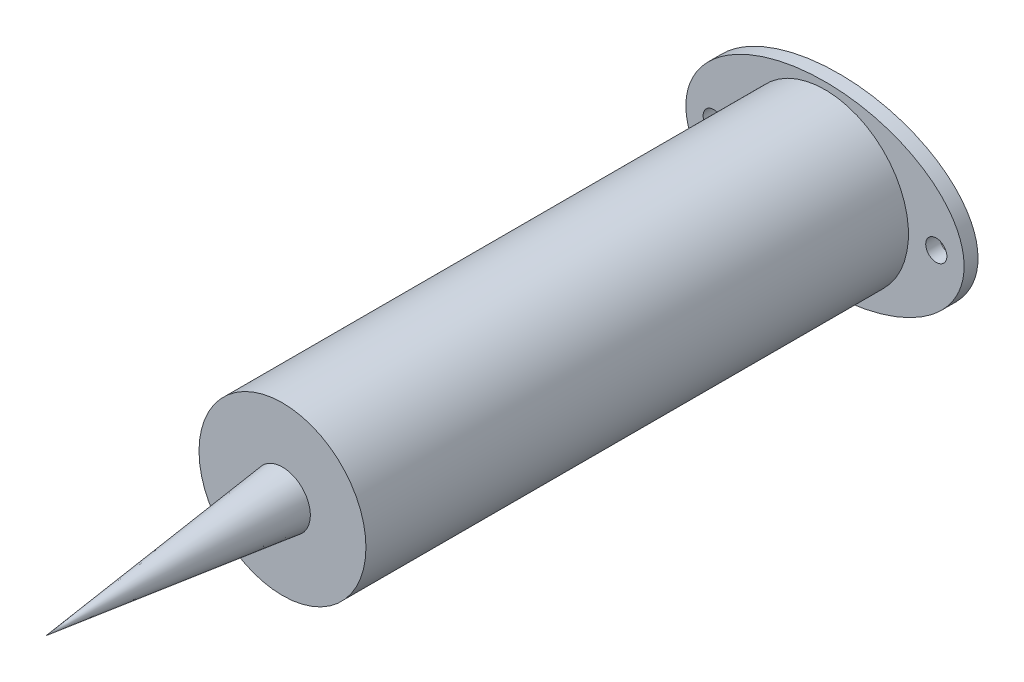
SolidWorks part; units mm, degrees
ref_plane "Front Plane" through (0, 0, 0) normal (0, 0, 1) x (1, 0, 0)
ref_plane "Top Plane" through (0, 0, 0) normal (0, 1, 0) x (1, 0, 0)
ref_plane "Right Plane" through (0, 0, 0) normal (1, 0, 0) x (0, 0, -1)
sketch "Sketch1" plane through (0, 0, 0) normal (0, 0, 1) x (1, 0, 0)
  circle A0 centre (0, 0) radius 17.4625
  circle A1 centre (0, 0) radius 19.05
  dimension "D1" = 34.925
  dimension "D2" = 38.1
extrude "Boss-Extrude1" add sketch "Sketch1" along normal blind 123.825
sketch "Sketch2" plane through (0, 0, 0) normal (0, 0, -1) x (-1, 0, 0)
  line L0 (0, 0) -> (-33.793, 0) construction
  line L1 (-33.793, 0) -> (0, 0) construction
  line L2 (0, 0) -> (0, 22.7795) construction
  line L3 (0, 0) -> (25.4, 0) construction
  circle A0 centre (0, 0) radius 17.4625
  circle A1 centre (0, 0) radius 19.05 construction
  circle A2 centre (25.4, 0) radius 2.413
  circle A3 centre (-25.4, 0) radius 2.413
  ellipse E0 centre (0, 0) end of major axis (31.75, 0) minor radius 20.6375
  dimension "D3" = 4.826
  dimension "D1" = 20.6375
  dimension "D2" = 63.5
  dimension "D4" = 25.4
  dimension "D5" = 25.4
extrude "Boss-Extrude2" add sketch "Sketch2" along normal blind 3.175
sketch "Sketch3" plane through (0, 0, 123.825) normal (0, 0, 1) x (1, 0, 0)
  circle A0 centre (0, 0) radius 17.4625
extrude "Boss-Extrude3" add sketch "Sketch3" against normal blind 4.953
sketch "Sketch4" plane through (0, 0, 0) normal (0, 1, 0) x (1, 0, 0)
  line L0 (0, -123.825) -> (0, -177.8)
  line L1 (-19.05, -123.825) -> (19.05, -123.825) construction
  line L2 (0, -177.8) -> (6.35, -123.825)
  line L3 (0, -123.825) -> (6.35, -123.825)
  line L4 (0, -123.825) -> (0, -188.666) construction
  dimension "D1" = 53.975
  dimension "D2" = 6.35
revolve "Revolve1" add sketch "Sketch4" angle 360 about L4
